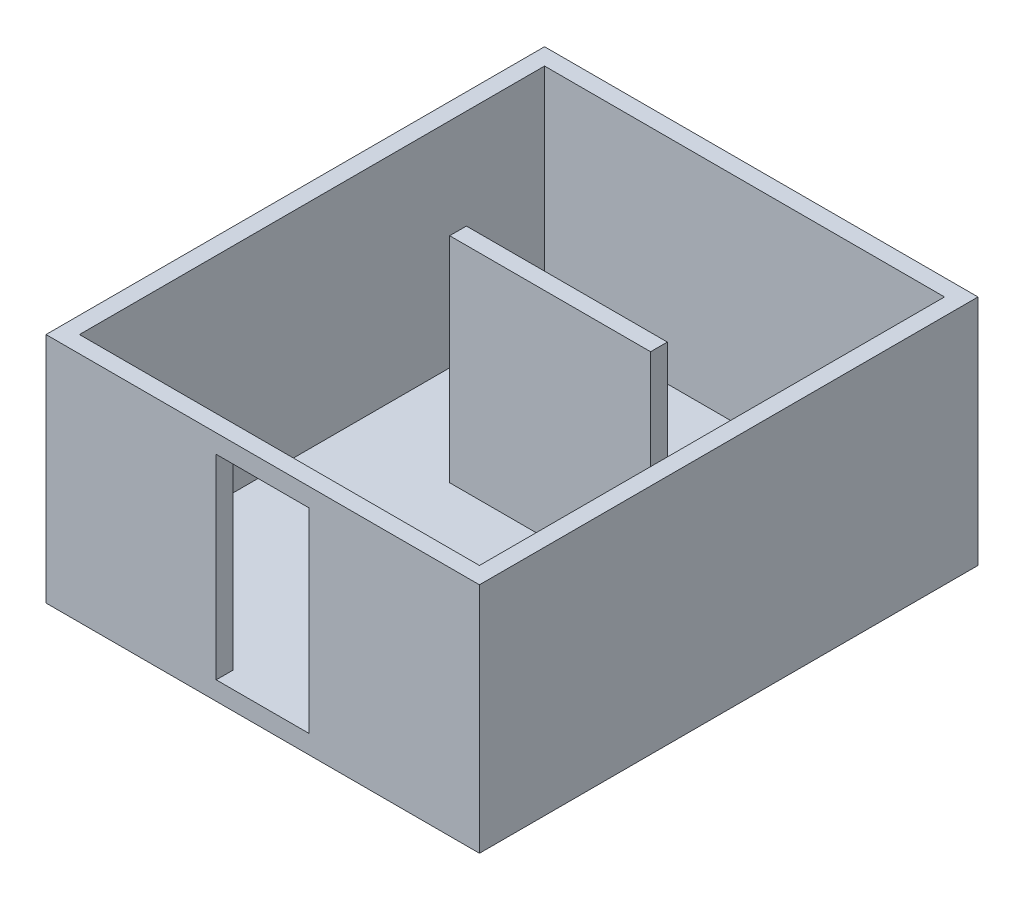
SolidWorks part; units mm, degrees
ref_plane "Alzado" through (0, 0, 0) normal (0, 0, 1) x (1, 0, 0)
ref_plane "Planta" through (0, 0, 0) normal (0, 1, 0) x (1, 0, 0)
ref_plane "Vista lateral" through (0, 0, 0) normal (1, 0, 0) x (0, 0, -1)
sketch "Croquis1" plane through (0, 0, 0) normal (0, 1, 0) x (1, 0, 0)
  line L1 (0, 0) -> (4660, 0)
  line L2 (0, 0) -> (0, -5360)
  line L3 (0, -5360) -> (4660, -5360)
  line L4 (4660, 0) -> (4660, -5360)
  dimension "D1" = 5360
  dimension "D2" = 4660
extrude "Saliente-Extruir1" add sketch "Croquis1" along normal blind 200
sketch "Croquis2" plane through (0, 200, 0) normal (0, 1, 0) x (1, 0, 0)
  line L0 (180, -180) -> (180, -5180)
  line L1 (0, 0) -> (4660, 0)
  line L2 (0, 0) -> (0, -5360)
  line L3 (0, -5360) -> (4660, -5360)
  line L4 (4660, 0) -> (4660, -5360)
  line L5 (180, -5180) -> (4480, -5180)
  line L6 (4480, -180) -> (4480, -5180)
  line L7 (180, -180) -> (4480, -180)
  line L8 (2330, -5180) -> (2330, -2180) construction
  line L10 (3410, -2270) -> (1250, -2270)
  line L11 (3410, -2270) -> (3410, -2090)
  line L12 (3410, -2090) -> (1250, -2090)
  line L13 (1250, -2270) -> (1250, -2090)
  line L14 (3410, -2270) -> (1250, -2090) construction
  line L15 (3410, -2090) -> (1250, -2270) construction
  line M1 (0, 0) -> (0, -5360)
  line M2 (0, -5360) -> (4660, -5360)
  line M3 (4660, -5360) -> (4660, 0)
  line M4 (4660, 0) -> (0, 0)
  dimension "D2" = 3000
  dimension "D3" = 180
  dimension "D4" = 2160
  dimension "D1" = 180
extrude "Saliente-Extruir2" add sketch "Croquis2" along normal blind 2300 contours L0 L7 L6 L5 M4 M1 M2 M3 | L13 L10 L11 L12
sketch "Croquis3" plane through (0, 0, 5360) normal (0, 0, 1) x (1, 0, 0)
  line L0 (2330, 200) -> (2330, 2500) construction
  line L1 (180, 200) -> (4480, 200) construction
  line L2 (0, 2500) -> (4660, 2500) construction
  line L4 (1830, 2300) -> (2830, 2300)
  line L5 (1830, 2300) -> (1830, 200)
  line L6 (1830, 200) -> (2830, 200)
  line L7 (2830, 2300) -> (2830, 200)
  line L8 (1830, 2300) -> (2830, 200) construction
  line L9 (1830, 200) -> (2830, 2300) construction
  point P6 (2330, 1250)
  dimension "D1" = 2100
  dimension "D2" = 1000
extrude "Cortar-Extruir1" cut sketch "Croquis3" against normal up to surface (180 mm away) up to face at (2330, 1350, 5180)
